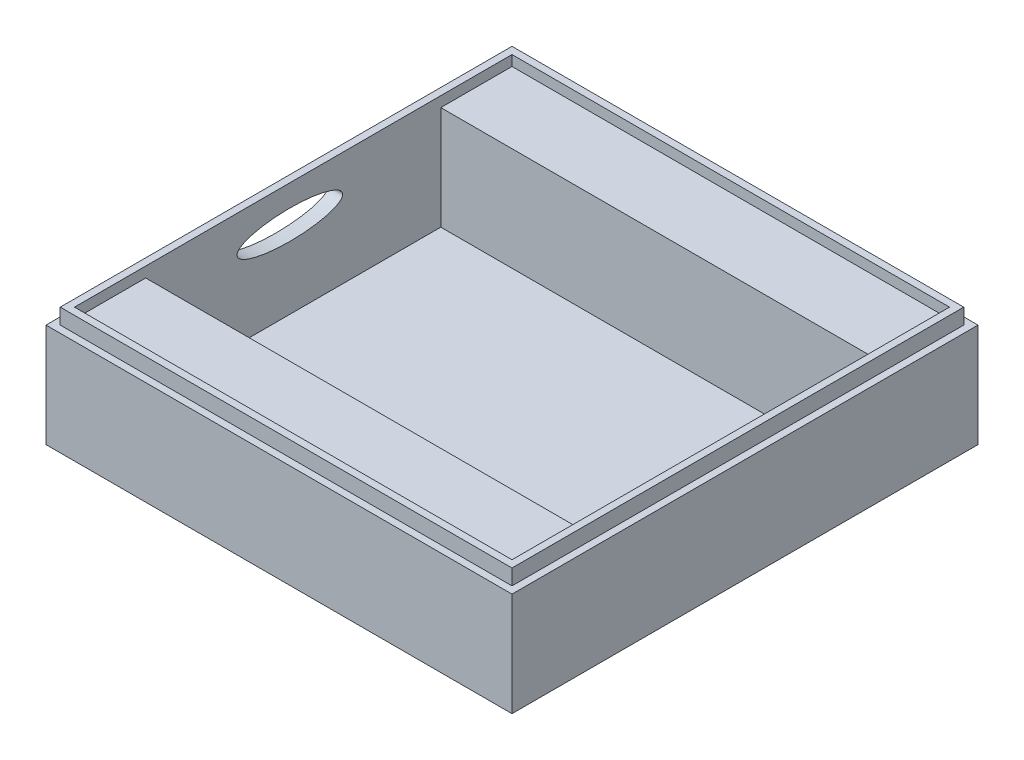
SolidWorks part; units mm, degrees
ref_plane "Front Plane" through (0, 0, 0) normal (0, 0, 1) x (1, 0, 0)
ref_plane "Top Plane" through (0, 0, 0) normal (0, 1, 0) x (1, 0, 0)
ref_plane "Right Plane" through (0, 0, 0) normal (1, 0, 0) x (0, 0, -1)
sketch "Sketch2" plane through (0, 0, 0) normal (0, 1, 0) x (1, 0, 0)
  line L1 (45, -45) -> (-45, -45)
  line L2 (45, -45) -> (45, 45)
  line L3 (45, 45) -> (-45, 45)
  line L4 (-45, -45) -> (-45, 45)
  line L5 (45, -45) -> (-45, 45) construction
  line L6 (45, 45) -> (-45, -45) construction
  point P0 (0, 0)
  dimension "D1" = 90
  dimension "D2" = 90
extrude "Boss-Extrude1" add sketch "Sketch2" along normal blind 20
sketch "Sketch5" plane through (0, 20, 0) normal (0, 1, 0) x (1, 0, 0)
  line L1 (-42.25, -42.25) -> (42.25, -42.25)
  line L2 (-42.25, -42.25) -> (-42.25, 42.25)
  line L3 (-42.25, 42.25) -> (42.25, 42.25)
  line L4 (42.25, -42.25) -> (42.25, 42.25)
  line L5 (-42.25, -42.25) -> (42.25, 42.25) construction
  line L6 (-42.25, 42.25) -> (42.25, -42.25) construction
  point P0 (0, 0)
  dimension "D1" = 84.5
  dimension "D2" = 84.5
extrude "Cut-Extrude2" cut sketch "Sketch5" against normal blind 13
sketch "Sketch10" plane through (0, 20, 0) normal (0, 1, 0) x (1, 0, 0)
  line L0 (-45, 0) -> (-42.25, 0)
  line L1 (-45, 45) -> (-45, -45) construction
  line L2 (-42.25, 42.25) -> (-42.25, -42.25) construction
sketch "Sketch13" plane through (0, 7, 0) normal (0, 1, 0) x (1, 0, 0)
  line L0 (42.25, -42.25) -> (42.25, 42.25) construction
  line L1 (-42.25, -28.5) -> (42.25, -28.5)
  line L2 (-42.25, -28.5) -> (-42.25, 28.5)
  line L3 (-42.25, 28.5) -> (42.25, 28.5)
  line L4 (42.25, -28.5) -> (42.25, 28.5)
  line L5 (-42.25, -28.5) -> (42.25, 28.5) construction
  line L6 (-42.25, 28.5) -> (42.25, -28.5) construction
  point P0 (0, 0)
  dimension "D1" = 84.5
  dimension "D2" = 57
extrude "Cut-Extrude5" cut sketch "Sketch13" against normal blind 6
sketch "Sketch14" plane through (0, 7, 0) normal (0, 1, 0) x (1, 0, 0)
  line L1 (-42.25, 42.25) -> (42.25, 42.25)
  line L2 (-42.25, 42.25) -> (-42.25, 28.5)
  line L3 (-42.25, 28.5) -> (42.25, 28.5)
  line L4 (42.25, 42.25) -> (42.25, 28.5)
  line L5 (42.25, -42.25) -> (-42.25, -42.25)
  line L6 (42.25, -42.25) -> (42.25, -28.5)
  line L7 (42.25, -28.5) -> (-42.25, -28.5)
  line L8 (-42.25, -42.25) -> (-42.25, -28.5)
sketch "Sketch17" plane through (-45, -8.202, 0) normal (-1, 0, 0) x (0, 0, 1)
  line L1 (0.6577, 25.1855) -> (0.6577, 23.1855) construction
  ellipse E0 centre (0.6577, 24.1855) end of major axis (-9.5385, 24.1855) minor radius 2.7936
  point P1 (0.6577, 24.1855)
  point P9 (0, 0)
  point P10 (7.2747, 30.7605)
  point P11 (0, 0)
  point P12 (0, 0)
  point P13 (10.854, 24.1855)
extrude "Cut-Extrude6" cut sketch "Sketch17" against normal blind 2.75
sketch "Sketch20" plane through (0, 20, 0) normal (0, 1, 0) x (1, 0, 0)
  line L0 (-45, 45) -> (-42.25, 42.25)
  line L1 (45, 45) -> (42.25, 42.25)
  line L2 (45, -45) -> (42.25, -42.25)
  line L3 (-45, -45) -> (-42.25, -42.25)
sketch "Sketch23" plane through (0, 1, 0) normal (0, 1, 0) x (1, 0, 0)
sketch "Sketch25" plane through (0, 7, 0) normal (0, 1, 0) x (1, 0, 0)
  line L1 (-42.25, 42.25) -> (42.25, 42.25)
  line L2 (-42.25, 42.25) -> (-42.25, 28.5)
  line L3 (-42.25, 28.5) -> (42.25, 28.5)
  line L4 (42.25, 42.25) -> (42.25, 28.5)
  line L5 (42.25, -42.25) -> (-42.25, -42.25)
  line L6 (42.25, -42.25) -> (42.25, -28.5)
  line L7 (42.25, -28.5) -> (-42.25, -28.5)
  line L8 (-42.25, -42.25) -> (-42.25, -28.5)
extrude "Boss-Extrude6" add sketch "Sketch25" along normal blind 14
sketch "Sketch27" plane through (0, 20, 0) normal (0, 1, 0) x (1, 0, 0)
  line L0 (-45, 45) -> (-42.25, 42.25) construction
  line L1 (-43.625, 43.625) -> (43.625, 43.625)
  line L2 (-43.625, 43.625) -> (-43.625, -43.625)
  line L3 (-43.625, -43.625) -> (43.625, -43.625)
  line L4 (43.625, 43.625) -> (43.625, -43.625)
  line L5 (45, -45) -> (42.25, -42.25) construction
  line L7 (-42.25, 42.25) -> (42.25, 42.25)
  line L8 (-42.25, 42.25) -> (-42.25, -42.25)
  line L9 (-42.25, -42.25) -> (42.25, -42.25)
  line L10 (42.25, 42.25) -> (42.25, -42.25)
extrude "Boss-Extrude8" add sketch "Sketch27" along normal blind 3
